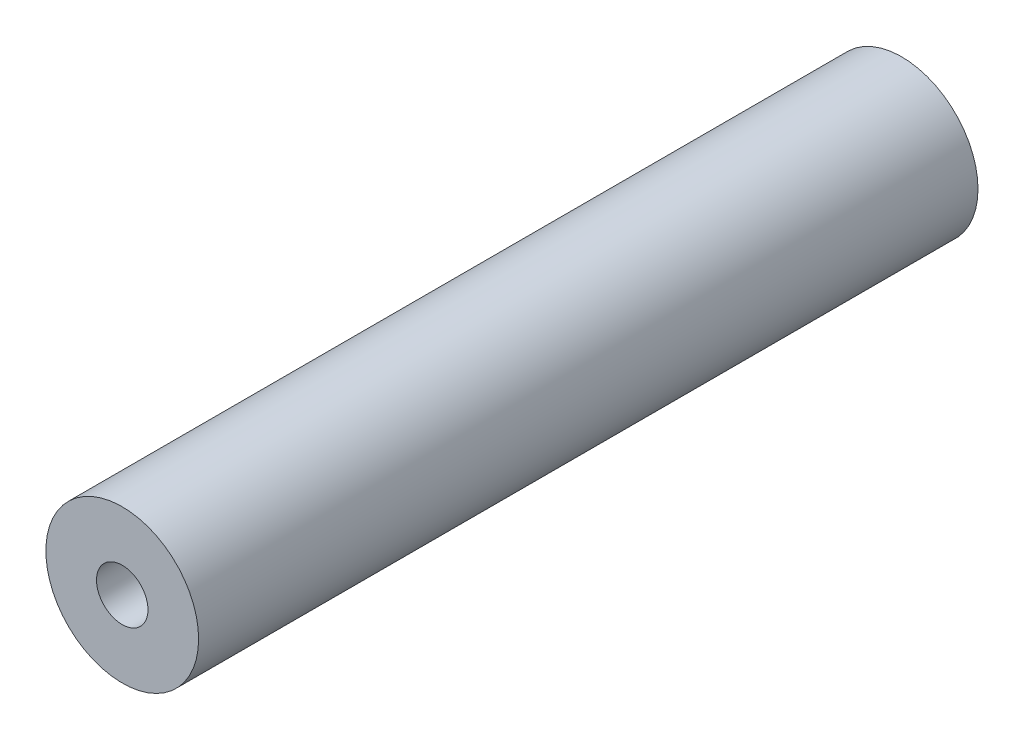
SolidWorks part; units mm, degrees
ref_plane "정면" through (0, 0, 0) normal (0, 0, 1) x (1, 0, 0)
ref_plane "윗면" through (0, 0, 0) normal (0, 1, 0) x (1, 0, 0)
ref_plane "우측면" through (0, 0, 0) normal (1, 0, 0) x (0, 0, -1)
sketch "스케치1" plane through (0, 0, 0) normal (0, 0, 1) x (1, 0, 0)
  circle A0 centre (0, 0) radius 4.9
  dimension "D1" = 9.8
extrude "보스-돌출1" add sketch "스케치1" along normal blind 50
hole_wizard "M4 나사 구멍1" positions "스케치2" profile "스케치3" tap size "M4" standard "ISO"
sketch "스케치2" plane through (0, 0, 50) normal (0, 0, 1) x (1, 0, 0)
  point P0 (0, 0)
sketch "스케치3" plane through (0, 0, 50) normal (1, 0, 0) x (0, -1, 0)
  line L0 (0, 0) -> (0, 12.4914)
  line L1 (0, 12.4914) -> (1.65, 11.5)
  line L2 (1.65, 11.5) -> (1.65, 0)
  line L5 (1.65, 0) -> (0, 0)
  line L10 (0, 12.4914) -> (-1.65, 11.5) construction
  line L11 (0, -6.35) -> (0, 107.95) construction
  dimension "탭 드릴 지름" = 3.3
  dimension "탭 드릴 깊이" = 11.5
  dimension "드릴 각도" = 118
cosmetic thread "구멍 나사산1" parameters "D1"=8, "D2"=4
hole_wizard "M4 나사 구멍2" positions "스케치4" profile "스케치5" tap size "M4" standard "ISO"
sketch "스케치4" plane through (0, 0, 0) normal (0, 0, -1) x (-1, 0, 0)
  point P0 (0, 0)
sketch "스케치5" plane through (0, 0, 0) normal (1, 0, 0) x (0, 1, 0)
  line L0 (0, 0) -> (0, 12.4914)
  line L1 (0, 12.4914) -> (1.65, 11.5)
  line L2 (1.65, 11.5) -> (1.65, 0)
  line L5 (1.65, 0) -> (0, 0)
  line L10 (0, 12.4914) -> (-1.65, 11.5) construction
  line L11 (0, -6.35) -> (0, 107.95) construction
  dimension "탭 드릴 지름" = 3.3
  dimension "탭 드릴 깊이" = 11.5
  dimension "드릴 각도" = 118
cosmetic thread "구멍 나사산2"
